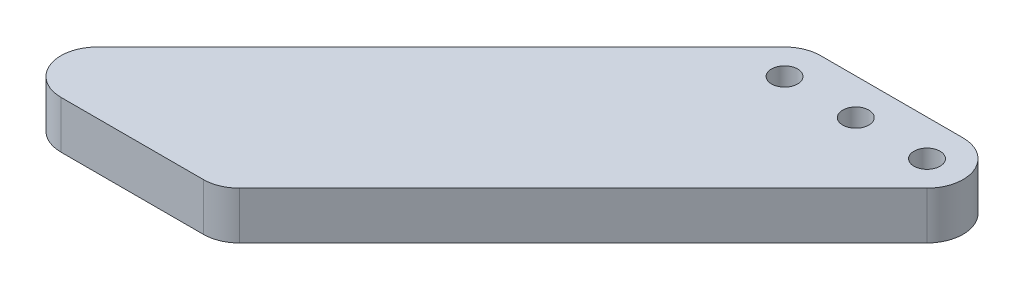
SolidWorks part; units mm, degrees
ref_plane "Front Plane" through (0, 0, 0) normal (0, 0, 1) x (1, 0, 0)
ref_plane "Top Plane" through (0, 0, 0) normal (0, 1, 0) x (1, 0, 0)
ref_plane "Right Plane" through (0, 0, 0) normal (1, 0, 0) x (0, 0, -1)
sketch "Sketch1" plane through (0, 0, 0) normal (0, 1, 0) x (1, 0, 0)
  line L0 (-15, 0) -> (15, 0) construction
  line L1 (0, 0) -> (0, 21.5455) construction
  line L2 (-15, 7.6) -> (15, 7.6)
  line L3 (-20.374, 5.374) -> (-105.748, -80)
  line L4 (-105.748, -80) -> (-54.252, -80)
  line L5 (-54.252, -80) -> (20.374, -5.374)
  circle A0 centre (15, 0) radius 2.6 construction
  circle A1 centre (-15, 0) radius 2.6 construction
  arc A2 (-15, 7.6) -> (-20.374, 5.374) centre (-15, 0) ccw
  arc A3 (15, 7.6) -> (20.374, -5.374) centre (15, 0) cw
  point P8 (0, 0)
  point P9 (-15, 0)
  point P10 (15, 0)
  dimension "D3" = 5.2
  dimension "D4" = 5
  dimension "D1" = 15
  dimension "D2" = 45
  dimension "D5" = 80
extrude "Boss-Extrude1" add sketch "Sketch1" along normal mid plane 10
fillet "Fillet1" radius 7.6 2 edges at (-54.252, 0, 80) (-105.748, 0, 80)
hole_wizard "M5 Clearance Hole1" positions "Sketch2" profile "Sketch3" hole size "M5" standard "ANSI Metric" end condition up to next
sketch "Sketch2" plane through (0, 5, 0) normal (0, 1, 0) x (1, 0, 0)
  point P0 (-15, 0)
  point P3 (0, 0)
  point P6 (15, 0)
sketch "Sketch3" plane through (-15, 5, 0) normal (1, 0, 0) x (0, 0, 1)
  line L0 (0, 0) -> (0, 10)
  line L1 (0, 10) -> (2.75, 10)
  line L2 (2.75, 10) -> (2.75, 0)
  line L5 (2.75, 0) -> (0, 0)
  line L11 (0, -6.35) -> (0, 107.95) construction
  dimension "Thru Hole Dia." = 5.5
  dimension "Thru Hole Depth" = 10
